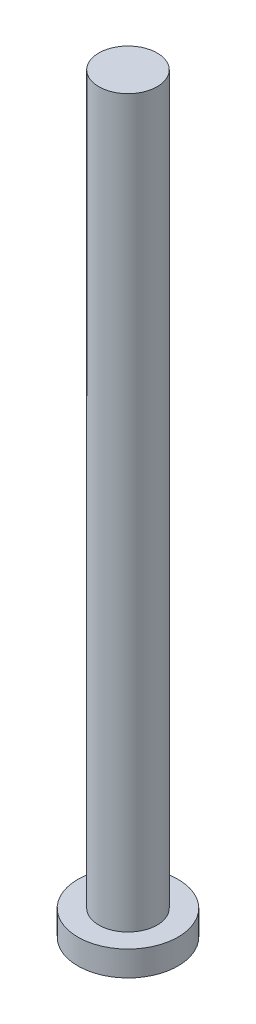
SolidWorks part; units mm, degrees
ref_plane "Ön Düzlem" through (0, 0, 0) normal (0, 0, 1) x (1, 0, 0)
ref_plane "Üst Düzlem" through (0, 0, 0) normal (0, 1, 0) x (1, 0, 0)
ref_plane "Sağ Düzlem" through (0, 0, 0) normal (1, 0, 0) x (0, 0, -1)
sketch "Çizim1" plane through (0, 0, 0) normal (0, 0, 1) x (1, 0, 0)
  line L0 (6, 90) -> (6, 0)
  line L1 (6, 0) -> (12, 0)
  line L4 (12, 0) -> (12, 3)
  line L5 (9.5, 3) -> (12, 3)
  line L7 (9.5, 3) -> (9.5, 90)
  line L8 (9.5, 90) -> (6, 90)
  dimension "D3" = 3
  dimension "D4" = 87
revolve "Döndür1" add sketch "Çizim1" angle 360 about L0
